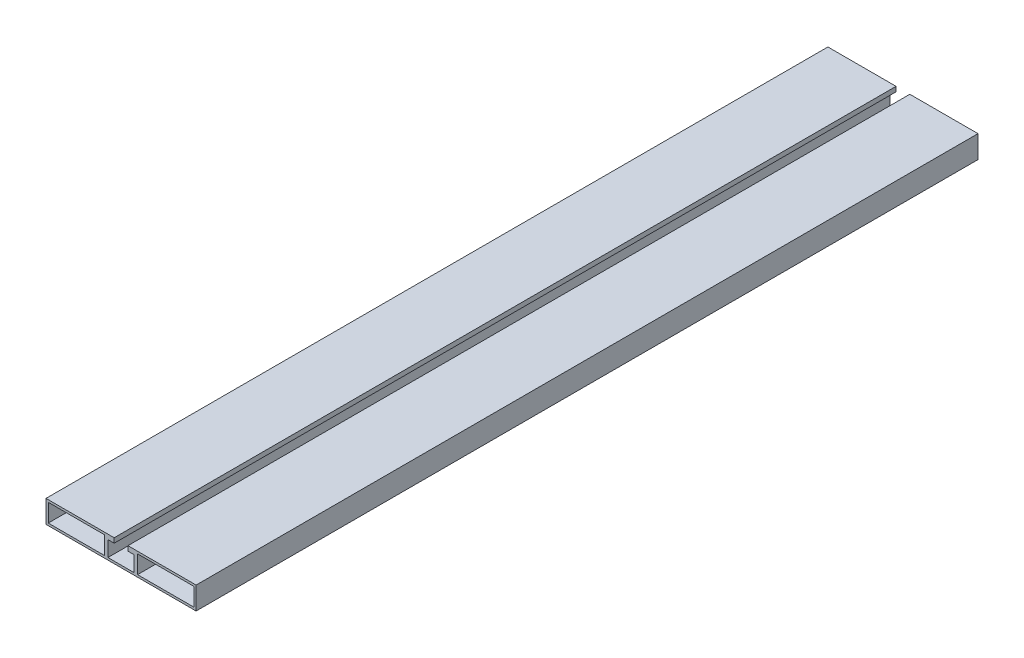
SolidWorks part; units mm, degrees
ref_plane "Front Plane" through (0, 0, 0) normal (0, 0, 1) x (1, 0, 0)
ref_plane "Top Plane" through (0, 0, 0) normal (0, 1, 0) x (1, 0, 0)
ref_plane "Right Plane" through (0, 0, 0) normal (1, 0, 0) x (0, 0, -1)
sketch "Sketch1" plane through (0, 0, 0) normal (0, 0, 1) x (1, 0, 0)
  line L0 (-10.5, 5.2) -> (-10.5, -7.2)
  line L1 (60, 9) -> (5.5, 9)
  line L3 (60, -9) -> (-60, -9)
  line L4 (-60, 9) -> (-60, -9)
  line L5 (-13.2, -7.2) -> (-13.2, 7.2)
  line L6 (-13.2, -7.2) -> (-58.2, -7.2)
  line L10 (-58.2, -7.2) -> (-58.2, 7.2)
  line L11 (-10.5, -7.2) -> (10.5, -7.2)
  line L12 (0, 9) -> (0, -9) construction
  line L13 (-5.5, 9) -> (-5.5, 5.2)
  line L14 (-5.5, 5.2) -> (-10.5, 5.2)
  line L16 (-13.2, 7.2) -> (-58.2, 7.2)
  line L17 (10.5, 5.2) -> (10.5, -7.2)
  line L18 (5.5, 5.2) -> (10.5, 5.2)
  line L19 (5.5, 9) -> (5.5, 5.2)
  line L20 (13.2, -7.2) -> (13.2, 7.2)
  line L21 (13.2, -7.2) -> (58.2, -7.2)
  line L22 (13.2, 7.2) -> (58.2, 7.2)
  line L23 (58.2, -7.2) -> (58.2, 7.2)
  line L24 (60, 9) -> (60, -9)
  line L25 (-5.5, 9) -> (-60, 9)
  point P0 (0, 0)
  point P3 (0, -7.2)
  point P6 (0, 0)
  point P26 (-5.5, 7.1)
  dimension "D1" = 60
  dimension "D2" = 18
  dimension "D3" = 54.5
  dimension "D4" = 1.8
  dimension "D5" = 45
  dimension "D6" = 10.5
  dimension "D7" = 1.8
  dimension "D8" = 3.8
  dimension "D9" = 1.8
  dimension "D10" = 1.8
extrude "Boss-Extrude1" add sketch "Sketch1" along normal blind 625
hole_wizard "Ø5.2 (5.2) Diameter Hole1" positions "Sketch2" profile "Sketch3" hole size "Ø5.2" standard "ISO" end condition through all
sketch "Sketch2" plane through (0, -9, 0) normal (0, -1, 0) x (-1, 0, 0)
  line L0 (60, -625) -> (-60, -625) construction
  line L1 (60, 0) -> (-60, 0) construction
  point P0 (0, -22)
  point P2 (0, -603)
  dimension "D1" = 22
  dimension "D2" = 22
sketch "Sketch3" plane through (0, -9, 22) normal (1, 0, 0) x (0, 0, -1)
  line L0 (0, 0) -> (0, 18)
  line L1 (0, 18) -> (2.6, 18)
  line L2 (2.6, 18) -> (2.6, 0)
  line L5 (2.6, 0) -> (0, 0)
  line L11 (0, -6.35) -> (0, 107.95) construction
  dimension "Thru Hole Dia." = 5.2
  dimension "Thru Hole Depth" = 18
